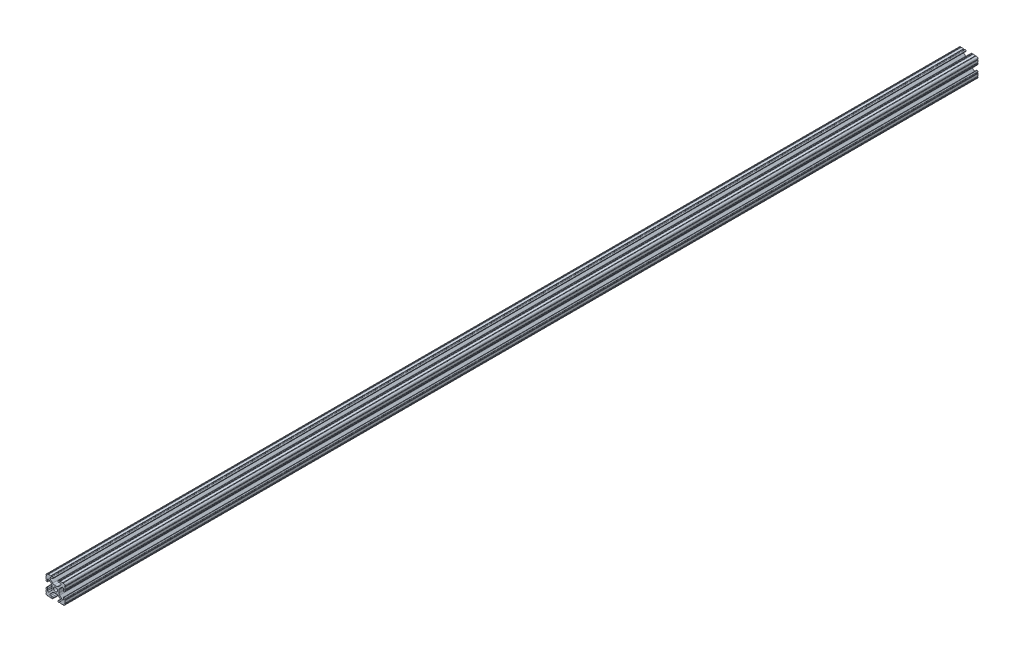
SolidWorks part; units mm, degrees
ref_plane "Front Plane" through (0, 0, 0) normal (0, 0, 1) x (1, 0, 0)
ref_plane "Top Plane" through (0, 0, 0) normal (0, 1, 0) x (1, 0, 0)
ref_plane "Right Plane" through (0, 0, 0) normal (1, 0, 0) x (0, 0, -1)
sketch "Sketch1" plane through (0, 0, 0) normal (0, 0, 1) x (1, 0, 0)
  line L88 (-7.1797, -8.6452) -> (-3.9523, -5.4237)
  line L89 (-1.7093, -4.4958) -> (1.7093, -4.4958)
  line L90 (3.9523, -5.4237) -> (7.1797, -8.6452)
  line L91 (6.4164, -10.4902) -> (4.2875, -10.4902)
  line L92 (3.2385, -11.5392) -> (3.2385, -11.651)
  line L93 (4.2875, -12.7) -> (5.3171, -12.7)
  line L94 (6.3331, -12.7) -> (9.5504, -12.7)
  line L95 (12.7, -9.5504) -> (12.7, -6.3331)
  line L96 (12.7, -5.3171) -> (12.7, -4.2875)
  line L97 (11.651, -3.2385) -> (11.5392, -3.2385)
  line L98 (10.4902, -4.2875) -> (10.4902, -6.4021)
  line L99 (8.7371, -7.1294) -> (5.441, -3.8408)
  line L100 (4.5085, -1.5932) -> (4.5085, 1.5932)
  line L101 (5.441, 3.8408) -> (8.7371, 7.1294)
  line L102 (10.4902, 6.4021) -> (10.4902, 4.2875)
  line L103 (11.5392, 3.2385) -> (11.651, 3.2385)
  line L104 (12.7, 4.2875) -> (12.7, 5.3171)
  line L105 (12.7, 6.3331) -> (12.7, 9.5504)
  line L106 (9.5504, 12.7) -> (6.3331, 12.7)
  line L107 (5.3171, 12.7) -> (4.2875, 12.7)
  line L108 (3.2385, 11.651) -> (3.2385, 11.5392)
  line L109 (4.2875, 10.4902) -> (6.4768, 10.4902)
  line L110 (7.207, 8.7244) -> (3.8983, 5.4232)
  line L111 (1.6558, 4.4958) -> (-1.6558, 4.4958)
  line L112 (-3.8983, 5.4232) -> (-7.207, 8.7244)
  line L113 (-6.4768, 10.4902) -> (-4.2875, 10.4902)
  line L114 (-3.2385, 11.5392) -> (-3.2385, 11.651)
  line L115 (-4.2875, 12.7) -> (-5.3171, 12.7)
  line L116 (-6.3331, 12.7) -> (-9.5504, 12.7)
  line L117 (-12.7, 9.5504) -> (-12.7, 6.3331)
  line L118 (-12.7, 5.3171) -> (-12.7, 4.2875)
  line L119 (-11.651, 3.2385) -> (-11.5392, 3.2385)
  line L120 (-10.4902, 4.2875) -> (-10.4902, 6.4021)
  line L121 (-8.7371, 7.1294) -> (-5.441, 3.8408)
  line L122 (-4.5085, 1.5932) -> (-4.5085, -1.5932)
  line L123 (-5.441, -3.8408) -> (-8.7371, -7.1294)
  line L124 (-10.4902, -6.4021) -> (-10.4902, -4.2875)
  line L125 (-11.5392, -3.2385) -> (-11.651, -3.2385)
  line L126 (-12.7, -4.2875) -> (-12.7, -5.3171)
  line L127 (-12.7, -6.3331) -> (-12.7, -9.5504)
  line L128 (-9.5504, -12.7) -> (-6.3331, -12.7)
  line L129 (-5.3171, -12.7) -> (-4.2875, -12.7)
  line L130 (-3.2385, -11.651) -> (-3.2385, -11.5392)
  line L131 (-4.2875, -10.4902) -> (-6.4164, -10.4902)
  circle A1 centre (0, 0) radius 2.6035
  arc A104 (-7.1797, -8.6452) -> (-6.4164, -10.4902) centre (-6.4164, -9.4098) ccw
  arc A105 (-1.7093, -4.4958) -> (-3.9523, -5.4237) centre (-1.7093, -7.6708) ccw
  arc A106 (3.9523, -5.4237) -> (1.7093, -4.4958) centre (1.7093, -7.6708) ccw
  arc A107 (6.4164, -10.4902) -> (7.1797, -8.6452) centre (6.4164, -9.4098) ccw
  arc A108 (4.2875, -10.4902) -> (3.2385, -11.5392) centre (4.2875, -11.5392) ccw
  arc A109 (3.2385, -11.651) -> (4.2875, -12.7) centre (4.2875, -11.651) ccw
  arc A110 (6.3331, -12.7) -> (5.3171, -12.7) centre (5.8251, -12.7) ccw
  arc A111 (10.5664, -12.6998) -> (9.5504, -12.7) centre (10.0584, -12.7) ccw
  arc A112 (10.5664, -12.6998) -> (12.6998, -10.5664) centre (10.5918, -10.5918) ccw
  arc A113 (12.7, -9.5504) -> (12.6998, -10.5664) centre (12.7, -10.0584) ccw
  arc A114 (12.7, -5.3171) -> (12.7, -6.3331) centre (12.7, -5.8251) ccw
  arc A115 (12.7, -4.2875) -> (11.651, -3.2385) centre (11.651, -4.2875) ccw
  arc A116 (11.5392, -3.2385) -> (10.4902, -4.2875) centre (11.5392, -4.2875) ccw
  arc A117 (8.7371, -7.1294) -> (10.4902, -6.4021) centre (9.4628, -6.4021) ccw
  arc A118 (4.5085, -1.5932) -> (5.441, -3.8408) centre (7.6835, -1.5932) ccw
  arc A119 (5.441, 3.8408) -> (4.5085, 1.5932) centre (7.6835, 1.5932) ccw
  arc A120 (10.4902, 6.4021) -> (8.7371, 7.1294) centre (9.4628, 6.4021) ccw
  arc A121 (10.4902, 4.2875) -> (11.5392, 3.2385) centre (11.5392, 4.2875) ccw
  arc A122 (11.651, 3.2385) -> (12.7, 4.2875) centre (11.651, 4.2875) ccw
  arc A123 (12.7, 6.3331) -> (12.7, 5.3171) centre (12.7, 5.8251) ccw
  arc A124 (12.6998, 10.5664) -> (12.7, 9.5504) centre (12.7, 10.0584) ccw
  arc A125 (12.6998, 10.5664) -> (10.5664, 12.6998) centre (10.5918, 10.5918) ccw
  arc A126 (9.5504, 12.7) -> (10.5664, 12.6998) centre (10.0584, 12.7) ccw
  arc A127 (5.3171, 12.7) -> (6.3331, 12.7) centre (5.8251, 12.7) ccw
  arc A128 (4.2875, 12.7) -> (3.2385, 11.651) centre (4.2875, 11.651) ccw
  arc A129 (3.2385, 11.5392) -> (4.2875, 10.4902) centre (4.2875, 11.5392) ccw
  arc A130 (7.207, 8.7244) -> (6.4768, 10.4902) centre (6.4768, 9.4563) ccw
  arc A131 (1.6558, 4.4958) -> (3.8983, 5.4232) centre (1.6558, 7.6708) ccw
  arc A132 (-3.8983, 5.4232) -> (-1.6558, 4.4958) centre (-1.6558, 7.6708) ccw
  arc A133 (-6.4768, 10.4902) -> (-7.207, 8.7244) centre (-6.4768, 9.4563) ccw
  arc A134 (-4.2875, 10.4902) -> (-3.2385, 11.5392) centre (-4.2875, 11.5392) ccw
  arc A135 (-3.2385, 11.651) -> (-4.2875, 12.7) centre (-4.2875, 11.651) ccw
  arc A136 (-6.3331, 12.7) -> (-5.3171, 12.7) centre (-5.8251, 12.7) ccw
  arc A137 (-10.5664, 12.6998) -> (-9.5504, 12.7) centre (-10.0584, 12.7) ccw
  arc A138 (-10.5664, 12.6998) -> (-12.6998, 10.5664) centre (-10.5918, 10.5918) ccw
  arc A139 (-12.7, 9.5504) -> (-12.6998, 10.5664) centre (-12.7, 10.0584) ccw
  arc A140 (-12.7, 5.3171) -> (-12.7, 6.3331) centre (-12.7, 5.8251) ccw
  arc A141 (-12.7, 4.2875) -> (-11.651, 3.2385) centre (-11.651, 4.2875) ccw
  arc A142 (-11.5392, 3.2385) -> (-10.4902, 4.2875) centre (-11.5392, 4.2875) ccw
  arc A143 (-8.7371, 7.1294) -> (-10.4902, 6.4021) centre (-9.4628, 6.4021) ccw
  arc A144 (-4.5085, 1.5932) -> (-5.441, 3.8408) centre (-7.6835, 1.5932) ccw
  arc A145 (-5.441, -3.8408) -> (-4.5085, -1.5932) centre (-7.6835, -1.5932) ccw
  arc A146 (-10.4902, -6.4021) -> (-8.7371, -7.1294) centre (-9.4628, -6.4021) ccw
  arc A147 (-10.4902, -4.2875) -> (-11.5392, -3.2385) centre (-11.5392, -4.2875) ccw
  arc A148 (-11.651, -3.2385) -> (-12.7, -4.2875) centre (-11.651, -4.2875) ccw
  arc A149 (-12.7, -6.3331) -> (-12.7, -5.3171) centre (-12.7, -5.8251) ccw
  arc A150 (-12.6998, -10.5664) -> (-12.7, -9.5504) centre (-12.7, -10.0584) ccw
  arc A151 (-12.6998, -10.5664) -> (-10.5664, -12.6998) centre (-10.5918, -10.5918) ccw
  arc A152 (-9.5504, -12.7) -> (-10.5664, -12.6998) centre (-10.0584, -12.7) ccw
  arc A153 (-5.3171, -12.7) -> (-6.3331, -12.7) centre (-5.8251, -12.7) ccw
  arc A154 (-4.2875, -12.7) -> (-3.2385, -11.651) centre (-4.2875, -11.651) ccw
  arc A155 (-3.2385, -11.5392) -> (-4.2875, -10.4902) centre (-4.2875, -11.5392) ccw
extrude "Boss-Extrude1" add sketch "Sketch1" along normal mid plane 1219.2
sketch "Sketch2" plane through (4.5085, 0, 0) normal (1, 0, 0) x (0, 0, -1)
  line L1 (0, 17.2111) -> (0, -17.5175) construction
  circle A0 centre (38.1, 0) radius 3.175
  circle A2 centre (-38.1, 0) radius 3.175
  circle A3 centre (0, 0) radius 3.175
  dimension "D1" = 6.35
  dimension "D2" = 38.1
  dimension "D3" = 6.35
  dimension "D4" = 6.35
  dimension "D6" = 76.2
extrude "Cut-Extrude1" cut sketch "Sketch2" against normal through all and the other way through all
sketch "Sketch3" plane through (0, 4.4958, 0) normal (0, 1, 0) x (1, 0, 0)
  line L0 (0, 0) -> (74.4467, 0) construction
  circle A0 centre (0, 330.2) radius 3.175
  circle A1 centre (0, -330.2) radius 3.175
  dimension "D1" = 6.35
  dimension "D2" = 330.2
extrude "Cut-Extrude2" cut sketch "Sketch3" against normal through all both and the other way through all
